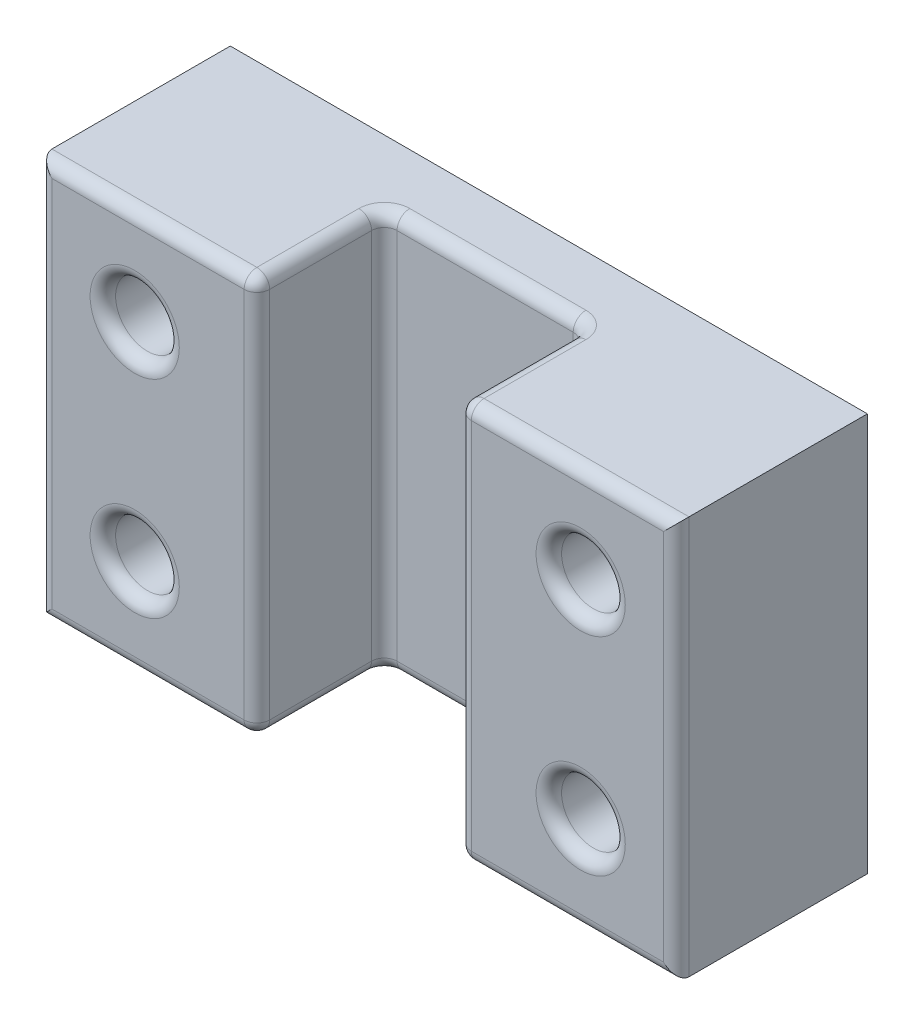
SolidWorks part; units mm, degrees
ref_plane "Front Plane" through (0, 0, 0) normal (0, 0, 1) x (1, 0, 0)
ref_plane "Top Plane" through (0, 0, 0) normal (0, 1, 0) x (1, 0, 0)
ref_plane "Right Plane" through (0, 0, 0) normal (1, 0, 0) x (0, 0, -1)
sketch "Sketch1" plane through (0, 0, 0) normal (0, 0, 1) x (1, 0, 0)
  line L0 (0, 0) -> (0, 34.5023) construction
  line L1 (-63.5, 39.7051) -> (63.5, 39.7051)
  line L2 (-63.5, 39.7051) -> (-63.5, -39.7051)
  line L3 (-63.5, -39.7051) -> (63.5, -39.7051)
  line L4 (63.5, 39.7051) -> (63.5, -39.7051)
  line L5 (-63.5, 39.7051) -> (63.5, -39.7051) construction
  line L6 (-63.5, -39.7051) -> (63.5, 39.7051) construction
  line L7 (0, 0) -> (-51.2344, 0) construction
  line L8 (0, 0) -> (41.9734, 0) construction
  circle A0 centre (-44.45, 20.6551) radius 6.35
  circle A1 centre (44.45, 20.6551) radius 6.35
  circle A2 centre (44.45, -20.6551) radius 6.35
  circle A3 centre (-44.45, -20.6551) radius 6.35
  point P0 (0, 0)
  dimension "D2" = 12.7
  dimension "D1" = 127
  dimension "D3" = 19.05
  dimension "D4" = 19.05
sketch "Sketch2" plane through (0, 0, 0) normal (0, 0, 1) x (1, 0, 0)
extrude "Boss-Extrude1" add sketch "Sketch1" along normal blind 38.1
sketch "Sketch3" plane through (0, 0, 38.1) normal (0, 0, 1) x (1, 0, 0)
  line L0 (-63.5, -39.7051) -> (63.5, -39.7051) construction
  line L1 (-20.0972, 39.7051) -> (20.0972, 39.7051)
  line L2 (-20.0972, 39.7051) -> (-20.0972, -39.7051)
  line L3 (-20.0972, -39.7051) -> (20.0972, -39.7051)
  line L4 (20.0972, 39.7051) -> (20.0972, -39.7051)
  line L5 (-20.0972, 39.7051) -> (20.0972, -39.7051) construction
  line L6 (-20.0972, -39.7051) -> (20.0972, 39.7051) construction
  point P0 (0, 0)
extrude "Cut-Extrude1" cut sketch "Sketch3" against normal blind 25.4
fillet "Fillet1" radius 2.54 18 edges at (-20.0972, -39.7051, 25.4) (20.0972, -39.7051, 25.4) (-20.0972, 39.7051, 25.4) (20.0972, 39.7051, 25.4) (-41.7986, -39.7051, 38.1) (-63.5, 0, 38.1) (-41.7986, 39.7051, 38.1) (-20.0972, 0, 38.1) (50.8, -20.6551, 38.1) (38.1, 20.6551, 38.1) (41.7986, 39.7051, 38.1) (63.5, 0, 38.1) (41.7986, -39.7051, 38.1) (20.0972, 0, 38.1) (0, -39.7051, 12.7) (-20.0972, 0, 12.7) (0, 39.7051, 12.7) (20.0972, 0, 12.7)
fillet "Fillet2" radius 2.54 2 edges at (-50.8, -20.6551, 38.1) (-38.1, 20.6551, 38.1)
